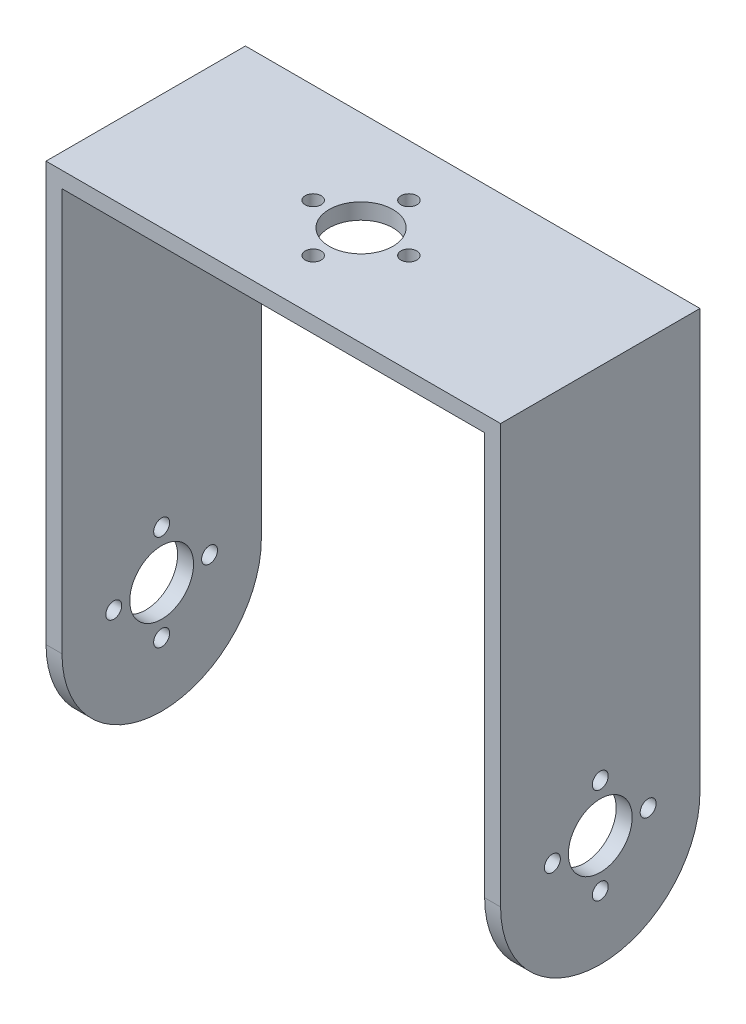
SolidWorks part; units mm, degrees
material "1060 Alloy"
ref_plane "Front Plane" through (0, 0, 0) normal (0, 0, 1) x (1, 0, 0)
ref_plane "Top Plane" through (0, 0, 0) normal (0, 1, 0) x (1, 0, 0)
ref_plane "Right Plane" through (0, 0, 0) normal (1, 0, 0) x (0, 0, -1)
sketch "Sketch3" plane through (0, 0, 0) normal (0, 0, 1) x (1, 0, 0)
  line L0 (-79.9255, 45.3865) -> (-27.043, 45.3865)
  line L1 (-81.9255, 45.3865) -> (-79.9255, 45.3865)
  line L2 (-81.9255, 45.3865) -> (-81.9255, -19.6135)
  line L3 (-81.9255, -19.6135) -> (-79.9255, -19.6135)
  line L4 (-79.9255, 43.39) -> (-79.9255, -19.6135)
  line L5 (-81.9255, 45.3865) -> (-79.9255, -19.6135) construction
  line L6 (-81.9255, -19.6135) -> (-79.9255, 45.3865) construction
  line L7 (-79.9255, 43.39) -> (-26.9255, 43.39)
  line L8 (-26.9255, 43.39) -> (-26.9255, -19.6135)
  line L9 (-27.043, 45.3865) -> (-24.9255, 45.3865)
  line L10 (-26.9255, -19.6135) -> (-24.9255, -19.6135)
  line L11 (-24.9255, 45.3865) -> (-24.9255, -19.6135)
  point P0 (-80.9255, 12.8865)
  dimension "D1" = 65
  dimension "D2" = 2
  dimension "D3" = 2
  dimension "D4" = 57
  dimension "D5" = 2
extrude "Boss-Extrude2" add sketch "Sketch3" along normal blind 25
sketch "Sketch4" plane through (0, 45.3865, 0) normal (0, 1, 0) x (1, 0, 0)
  line L0 (-81.9255, -25) -> (-81.9255, 0) construction
  line L3 (-24.9255, -25) -> (-81.9255, -25) construction
  circle A0 centre (-54.9255, -12.5) radius 4
  dimension "D1" = 27
  dimension "D3" = 8
  dimension "D2" = 12.5
extrude "Cut-Extrude1" cut sketch "Sketch4" against normal through all
sketch "Sketch6" plane through (-81.9255, 0, 0) normal (-1, 0, 0) x (0, 0, 1)
  line L1 (25, 45.3865) -> (0, 45.3865) construction
  line L2 (0, 45.3865) -> (0, -19.6135) construction
  circle A0 centre (12.5, -5.6135) radius 4
  dimension "D1" = 51
  dimension "D2" = 12.5
extrude "Cut-Extrude2" cut sketch "Sketch6" against normal through all
sketch "Sketch8" plane through (-81.9255, 0, 0) normal (-1, 0, 0) x (0, 0, 1)
  line L0 (25, 45.3865) -> (25, -19.6135) construction
  line L1 (25, -19.6135) -> (0, -19.6135) construction
  line L2 (0, 45.3865) -> (0, -19.6135) construction
  line L3 (25, -19.6135) -> (0, -19.6135)
  line L4 (0, 45.3865) -> (0, -19.6135)
  line L5 (25, 45.3865) -> (25, -19.6135)
  circle A0 centre (12.5, -7.1135) radius 12.5
  line M4 (0, -19.6135) -> (25, -19.6135)
  line M5 (25, -19.6135) -> (25, 45.3865)
extrude "Cut-Extrude3" cut sketch "Sketch8" against normal through all contours A0 L4 M4 | A0 L3 M5
sketch "Sketch9" plane through (-24.9255, 0, 0) normal (1, 0, 0) x (0, 0, -1)
  circle A0 centre (-12.5, -11.6186) radius 1
  circle A2 centre (-18.5051, -5.6135) radius 1
  circle A3 centre (-6.4949, -5.6135) radius 1
  circle A4 centre (-12.5, 0.3916) radius 1
  circle A5 centre (-12.5, -5.6135) radius 6.0051 construction
  point P13 (-12.5, -5.6135)
  point P15 (-12.5, -5.6135)
  dimension "D1" = 4
  dimension "D3" = 2
  dimension "D2" = 6.0051
extrude "Cut-Extrude4" cut sketch "Sketch9" against normal through all
sketch "Sketch10" plane through (0, 45.3865, 0) normal (0, 1, 0) x (1, 0, 0)
  circle A0 centre (-48.9255, -12.5) radius 1
  circle A1 centre (-54.9255, -12.5) radius 6 construction
  circle A2 centre (-54.9255, -6.5) radius 1
  circle A3 centre (-54.9255, -18.5) radius 1
  circle A4 centre (-60.9255, -12.5) radius 1
  point P13 (-54.9255, -12.5)
  point P16 (-54.9255, -12.5)
  dimension "D1" = 4
  dimension "D3" = 12
  dimension "D5" = 2
extrude "Cut-Extrude5" cut sketch "Sketch10" against normal through all
